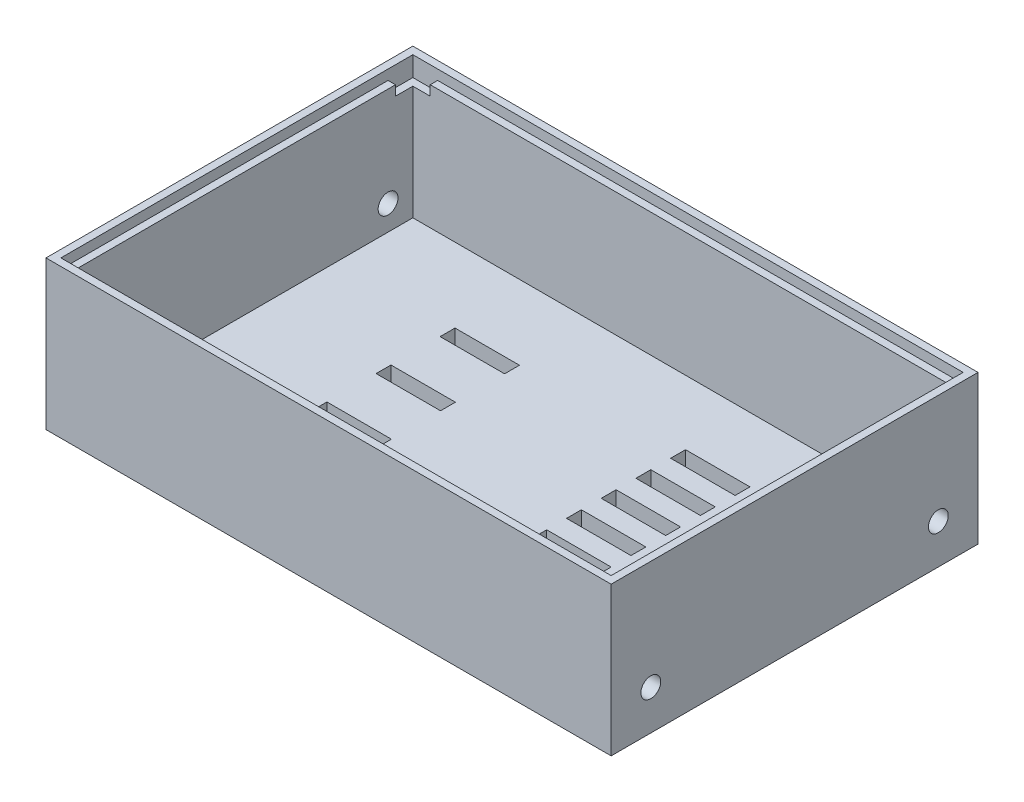
SolidWorks part; units mm, degrees
ref_plane "Plano frontal" through (0, 0, 0) normal (0, 0, 1) x (1, 0, 0)
ref_plane "Plano superior" through (0, 0, 0) normal (0, 1, 0) x (1, 0, 0)
ref_plane "Plano direito" through (0, 0, 0) normal (1, 0, 0) x (0, 0, -1)
sketch "Sketch1" plane through (0, 0, 0) normal (0, 1, 0) x (1, 0, 0)
  line L0 (54, 34) -> (-54, -34) construction
  line L1 (-54, 34) -> (54, 34)
  line L2 (-54, 34) -> (-54, -34)
  line L3 (-54, -34) -> (54, -34)
  line L4 (54, 34) -> (54, -34)
  line L5 (0, 0) -> (0, 34) construction
  line L6 (0, 0) -> (-54, 0) construction
  point P7 (-49.1, 31.1)
  point P8 (-51.1, 26.1)
  dimension "D1" = 108
  dimension "D2" = 68
  dimension "D4" = 2.9
  dimension "D5" = 2.9
extrude "Boss-Extrude1" add sketch "Sketch1" along normal blind 3
sketch "Sketch2" plane through (0, 3, 0) normal (0, 1, 0) x (1, 0, 0)
  line L0 (-57, 37) -> (-57, -37)
  line L1 (-57, -37) -> (57, -37)
  line L2 (57, -37) -> (57, 37)
  line L3 (57, 37) -> (-57, 37)
  line L4 (-54, 34) -> (-54, -34)
  line L5 (-54, -34) -> (54, -34)
  line L6 (54, -34) -> (54, 34)
  line L7 (54, 34) -> (-54, 34)
  line L8 (-54, 34) -> (-54, -34)
  line L9 (-54, -34) -> (54, -34)
  line L10 (54, -34) -> (54, 34)
  line L11 (54, 34) -> (-54, 34)
  dimension "D1" = 0
  dimension "D2" = 3
extrude "Boss-Extrude2" add sketch "Sketch2" along normal blind 25 and the other way blind 3
sketch "Sketch4" plane through (0, 28, 0) normal (0, 1, 0) x (1, 0, 0)
  line L0 (-55.5, 35.5) -> (-55.5, -35.5)
  line L5 (-55.5, -35.5) -> (55.5, -35.5)
  line L6 (55.5, 35.5) -> (55.5, -35.5)
  line L7 (-55.5, 35.5) -> (55.5, 35.5)
  line L13 (-57, 37) -> (57, 37)
  line L14 (-57, 37) -> (-57, -37)
  line L15 (-57, -37) -> (57, -37)
  line L16 (57, 37) -> (57, -37)
  dimension "D1" = 1.5
  dimension "D2" = 1.5
  dimension "D3" = 1.5
  dimension "D4" = 1.5
extrude "Boss-Extrude3" add sketch "Sketch4" along normal blind 2
sketch "Sketch5" plane through (-54, 0, 0) normal (1, 0, 0) x (0, 0, -1)
  line L0 (34, 3) -> (34, 28) construction
  line L1 (34, 3) -> (-34, 3) construction
  circle A0 centre (29, 8) radius 2
  dimension "D1" = 4
  dimension "D2" = 5
  dimension "D3" = 5
extrude "Cut-Extrude1" cut sketch "Sketch5" against normal through all
sketch "Sketch6" plane through (0, 0, 0) normal (0, -1, 0) x (1, 0, 0)
  line L0 (-57, 37) -> (57, 37) construction
  line L1 (14, 24) -> (27, 24)
  line L2 (14, 24) -> (14, 21)
  line L3 (14, 21) -> (27, 21)
  line L4 (44, 24) -> (44, 21)
  line L5 (57, 37) -> (57, -37) construction
  line L6 (31, 24) -> (44, 24)
  line L8 (27, 24) -> (27, 21)
  line L10 (31, 24) -> (31, 21)
  line L11 (31, 21) -> (44, 21)
  line L12 (14, 17) -> (27, 17)
  line L13 (14, 17) -> (14, 14)
  line L14 (14, 14) -> (27, 14)
  line L15 (44, 17) -> (44, 14)
  line L16 (31, 17) -> (44, 17)
  line L17 (27, 17) -> (27, 14)
  line L18 (31, 17) -> (31, 14)
  line L19 (31, 14) -> (44, 14)
  line L20 (14, 10) -> (27, 10)
  line L21 (14, 10) -> (14, 7)
  line L22 (14, 7) -> (27, 7)
  line L23 (44, 10) -> (44, 7)
  line L24 (31, 10) -> (44, 10)
  line L25 (27, 10) -> (27, 7)
  line L26 (31, 10) -> (31, 7)
  line L27 (31, 7) -> (44, 7)
  line L28 (14, 3) -> (27, 3)
  line L29 (14, 3) -> (14, 0)
  line L30 (14, 0) -> (27, 0)
  line L31 (44, 3) -> (44, 0)
  line L32 (31, 3) -> (44, 3)
  line L33 (27, 3) -> (27, 0)
  line L34 (31, 3) -> (31, 0)
  line L35 (31, 0) -> (44, 0)
  line L36 (14, -4) -> (27, -4)
  line L37 (14, -4) -> (14, -7)
  line L38 (14, -7) -> (27, -7)
  line L39 (44, -4) -> (44, -7)
  line L40 (31, -4) -> (44, -4)
  line L41 (27, -4) -> (27, -7)
  line L42 (31, -4) -> (31, -7)
  line L43 (31, -7) -> (44, -7)
  line L44 (14, -11) -> (27, -11)
  line L45 (14, -11) -> (14, -14)
  line L46 (14, -14) -> (27, -14)
  line L47 (44, -11) -> (44, -14)
  line L48 (31, -11) -> (44, -11)
  line L49 (27, -11) -> (27, -14)
  line L50 (31, -11) -> (31, -14)
  line L51 (31, -14) -> (44, -14)
  line L52 (14, -18) -> (27, -18)
  line L53 (14, -18) -> (14, -21)
  line L54 (14, -21) -> (27, -21)
  line L55 (44, -18) -> (44, -21)
  line L56 (31, -18) -> (44, -18)
  line L57 (27, -18) -> (27, -21)
  line L58 (31, -18) -> (31, -21)
  line L59 (31, -21) -> (44, -21)
  point P12 (44, 22.5)
  dimension "D1" = 3
  dimension "D2" = 30
  dimension "D3" = 13
  dimension "D4" = 13
  dimension "D5" = 13
  dimension "D6" = 13
  dimension "D7" = 7
extrude "Cut-Extrude2" cut sketch "Sketch6" against normal through all
mirror "Mirror1" about plane through (0, 0, 0) normal (0, 0, 1) of "Cut-Extrude1"
mirror "Mirror2" about plane through (0, 0, 0) normal (1, 0, 0) of "Mirror1", "Cut-Extrude1"
sketch "Sketch7" plane through (0, 3, 0) normal (0, 1, 0) x (1, 0, 0)
  line L1 (-30.5, 19) -> (-17.5, 19)
  line L2 (-30.5, 19) -> (-30.5, 16)
  line L3 (-30.5, 16) -> (-17.5, 16)
  line L4 (-17.5, 19) -> (-17.5, 16)
  line L5 (54, 34) -> (-54, 34) construction
  line L6 (-30.5, 6.0834) -> (-17.5, 6.0834)
  line L7 (-30.5, 6.0834) -> (-30.5, 3.0834)
  line L8 (-30.5, 3.0834) -> (-17.5, 3.0834)
  line L9 (-17.5, 6.0834) -> (-17.5, 3.0834)
  line L10 (-30.5, -6.8332) -> (-17.5, -6.8332)
  line L11 (-30.5, -6.8332) -> (-30.5, -9.8332)
  line L12 (-30.5, -9.8332) -> (-17.5, -9.8332)
  line L13 (-17.5, -6.8332) -> (-17.5, -9.8332)
  line L14 (-30.5, -19.7498) -> (-17.5, -19.7498)
  line L15 (-30.5, -19.7498) -> (-30.5, -22.7498)
  line L16 (-30.5, -22.7498) -> (-17.5, -22.7498)
  line L17 (-17.5, -19.7498) -> (-17.5, -22.7498)
  line L18 (55.5, -35.5) -> (55.5, 35.5) construction
  point P4 (-24, 16)
  point P14 (-24, 3.0834)
  point P19 (-24, -9.8332)
  point P24 (-24, -22.7498)
  dimension "D1" = 13
  dimension "D2" = 3
  dimension "D3" = 4
  dimension "D4" = 15
  dimension "D5" = 73
extrude "Cut-Extrude3" cut sketch "Sketch7" against normal blind 10
sketch "Sketch8" plane through (0, 28, 0) normal (0, 1, 0) x (1, 0, 0)
  line L0 (-54, 34) -> (-50.5, 34)
  line L1 (-55.5, 35.5) -> (-50.5, 35.5)
  line L2 (-55.5, 35.5) -> (-55.5, 30.5)
  line L3 (-55.5, 30.5) -> (-54, 30.5)
  line L4 (-50.5, 35.5) -> (-50.5, 34)
  line L8 (-54, 30.5) -> (-54, 34)
  line L10 (54, -34) -> (54, -30.5)
  line L11 (55.5, -35.5) -> (50.5, -35.5)
  line L12 (55.5, -35.5) -> (55.5, -30.5)
  line L13 (55.5, -30.5) -> (54, -30.5)
  line L14 (50.5, -35.5) -> (50.5, -34)
  line L18 (50.5, -34) -> (54, -34)
  dimension "D1" = 5
  dimension "D2" = 5
  dimension "D3" = 5
  dimension "D4" = 5
extrude "Cut-Extrude4" cut sketch "Sketch8" against normal blind 2
